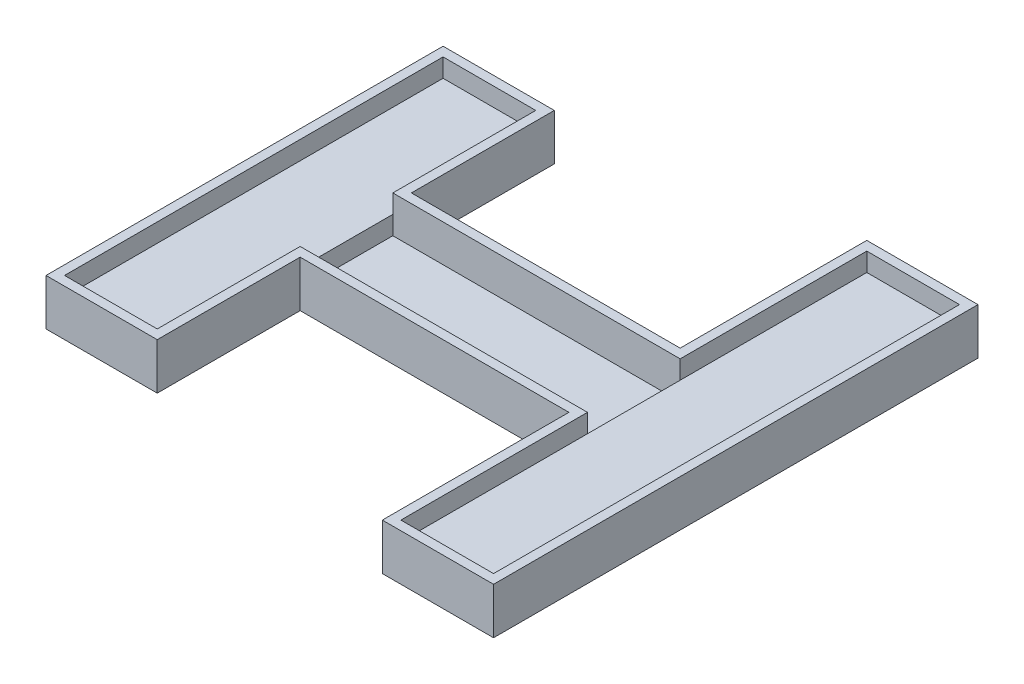
SolidWorks part; units mm, degrees
ref_plane "前视基准面" through (0, 0, 0) normal (0, 0, 1) x (1, 0, 0)
ref_plane "上视基准面" through (0, 0, 0) normal (0, 1, 0) x (1, 0, 0)
ref_plane "右视基准面" through (0, 0, 0) normal (1, 0, 0) x (0, 0, -1)
other "Configuration Table"
sketch "草图1" plane through (0, 0, 0) normal (0, 1, 0) x (1, 0, 0)
  line L1 (-15.5, -5) -> (15.5, -5)
  line L2 (-15.5, -5) -> (-15.5, 5)
  line L3 (-15.5, 5) -> (15.5, 5)
  line L4 (15.5, -5) -> (15.5, 5)
  line L5 (-15.5, -5) -> (15.5, 5) construction
  line L6 (-15.5, 5) -> (15.5, -5) construction
  line L7 (15.5, 5) -> (25.5, 5)
  line L8 (15.5, 5) -> (15.5, -5)
  line L9 (15.5, -5) -> (25.5, -5)
  line L10 (25.5, 5) -> (25.5, -5)
  line L11 (-15.5, 5) -> (-25.5, 5)
  line L12 (-15.5, 5) -> (-15.5, -5)
  line L13 (-15.5, -5) -> (-25.5, -5)
  line L14 (-25.5, 5) -> (-25.5, -5)
  line L15 (-25.5, -5) -> (-15.5, -5)
  line L16 (-25.5, -5) -> (-25.5, -20.42)
  line L17 (-25.5, -20.42) -> (-15.5, -20.42)
  line L18 (-15.5, -5) -> (-15.5, -20.42)
  line L19 (-25.5, 5) -> (-15.5, 5)
  line L20 (-25.5, 5) -> (-25.5, 20.42)
  line L21 (-25.5, 20.42) -> (-15.5, 20.42)
  line L22 (-15.5, 5) -> (-15.5, 20.42)
  line L23 (25.5, -5) -> (15.5, -5)
  line L24 (25.5, -5) -> (25.5, -25.133)
  line L25 (25.5, -25.133) -> (15.5, -25.133)
  line L26 (15.5, -5) -> (15.5, -25.133)
  line L27 (25.5, 5) -> (15.5, 5)
  line L28 (25.5, 5) -> (25.5, 25.133)
  line L29 (25.5, 25.133) -> (15.5, 25.133)
  line L30 (15.5, 5) -> (15.5, 25.133)
  point P0 (0, 0)
  dimension "D1" = 10
  dimension "D2" = 31
  dimension "D3" = 10
  dimension "D4" = 10
  dimension "D5" = 10
  dimension "D6" = 10
  dimension "D7" = 20.133
  dimension "D8" = 20.133
  dimension "D9" = 15.42
  dimension "D10" = 15.42
extrude "凸台-拉伸1" add sketch "草图1" along normal blind 1 contours L11 L22 L21 L20 | L11 L14 L13 L2 | L18 L13 L16 L17 | L1 L4 L3 L2 | L30 L7 L28 L29 | L10 L7 L4 L9 | L9 L26 L25 L24
sketch "草图2" plane through (0, 1, 0) normal (0, 1, 0) x (1, 0, 0)
  line L0 (-26.5, 21.42) -> (-26.5, -21.42)
  line L1 (-26.5, -21.42) -> (-14.5, -21.42)
  line L2 (-14.5, -21.42) -> (-14.5, -6)
  line L3 (-14.5, -6) -> (14.5, -6)
  line L4 (14.5, -6) -> (14.5, -26.133)
  line L5 (14.5, -26.133) -> (26.5, -26.133)
  line L6 (26.5, -26.133) -> (26.5, 26.133)
  line L7 (26.5, 26.133) -> (14.5, 26.133)
  line L8 (14.5, 26.133) -> (14.5, 6)
  line L9 (14.5, 6) -> (-14.5, 6)
  line L10 (-14.5, 6) -> (-14.5, 21.42)
  line L11 (-14.5, 21.42) -> (-26.5, 21.42)
  line L12 (-25.5, 20.42) -> (-25.5, -20.42)
  line L13 (-25.5, -20.42) -> (-15.5, -20.42)
  line L14 (-15.5, -20.42) -> (-15.5, -5)
  line L15 (-15.5, -5) -> (15.5, -5)
  line L16 (15.5, -5) -> (15.5, -25.133)
  line L17 (15.5, -25.133) -> (25.5, -25.133)
  line L18 (25.5, -25.133) -> (25.5, 25.133)
  line L19 (25.5, 25.133) -> (15.5, 25.133)
  line L20 (15.5, 25.133) -> (15.5, 5)
  line L21 (-15.5, -5) -> (15.5, -5)
  line L22 (-15.5, 5) -> (-15.5, 20.42)
  line L23 (-15.5, 20.42) -> (-25.5, 20.42)
  line L24 (-25.5, 20.42) -> (-25.5, -20.42)
  line L25 (-25.5, -20.42) -> (-15.5, -20.42)
  line L26 (-15.5, -20.42) -> (-15.5, -5)
  line L28 (15.5, -5) -> (15.5, -25.133)
  line L29 (15.5, -25.133) -> (25.5, -25.133)
  line L30 (25.5, -25.133) -> (25.5, 25.133)
  line L31 (25.5, 25.133) -> (15.5, 25.133)
  line L32 (15.5, 25.133) -> (15.5, 5)
  line L34 (-15.5, 5) -> (-15.5, 20.42)
  line L35 (-15.5, 20.42) -> (-25.5, 20.42)
  line L48 (-15.5, -5) -> (15.5, -5) construction
  line L49 (15.5, 5) -> (-15.5, 5) construction
  line L50 (15.5, 5) -> (-15.5, 5)
  line L51 (15.5, 5) -> (-15.5, 5)
  dimension "D1" = 0
  dimension "D2" = 1
extrude "凸台-拉伸2" add sketch "草图2" along normal blind 4 and the other way blind 1 separate body
sketch "草图3" plane through (0, 1, 0) normal (0, 1, 0) x (1, 0, 0)
  line L0 (-15.5, 5) -> (-15.5, -5)
  line L1 (15.5, 5) -> (15.5, -5)
  line L12 (-25.5, 20.42) -> (-25.5, -20.42)
  line L13 (-25.5, -20.42) -> (-15.5, -20.42)
  line L14 (-15.5, -20.42) -> (-15.5, -5)
  line L15 (-15.5, -5) -> (15.5, -5)
  line L16 (15.5, -5) -> (15.5, -25.133)
  line L17 (15.5, -25.133) -> (25.5, -25.133)
  line L18 (25.5, -25.133) -> (25.5, 25.133)
  line L19 (25.5, 25.133) -> (15.5, 25.133)
  line L20 (15.5, 25.133) -> (15.5, 5)
  line L21 (-15.5, -5) -> (15.5, -5)
  line L22 (-15.5, 5) -> (-15.5, 20.42)
  line L23 (-15.5, 20.42) -> (-25.5, 20.42)
  line L24 (-25.5, 20.42) -> (-25.5, -20.42)
  line L25 (-25.5, -20.42) -> (-15.5, -20.42)
  line L26 (-15.5, -20.42) -> (-15.5, -5)
  line L28 (15.5, -5) -> (15.5, -25.133)
  line L29 (15.5, -25.133) -> (25.5, -25.133)
  line L30 (25.5, -25.133) -> (25.5, 25.133)
  line L31 (25.5, 25.133) -> (15.5, 25.133)
  line L32 (15.5, 25.133) -> (15.5, 5)
  line L34 (-15.5, 5) -> (-15.5, 20.42)
  line L35 (-15.5, 20.42) -> (-25.5, 20.42)
  line L38 (15.5, 5) -> (-15.5, 5)
  line L39 (15.5, 5) -> (-15.5, 5)
  dimension "D2" = 0
  dimension "D1" = 0
extrude "凸台-拉伸3" add sketch "草图3" along normal blind 2
